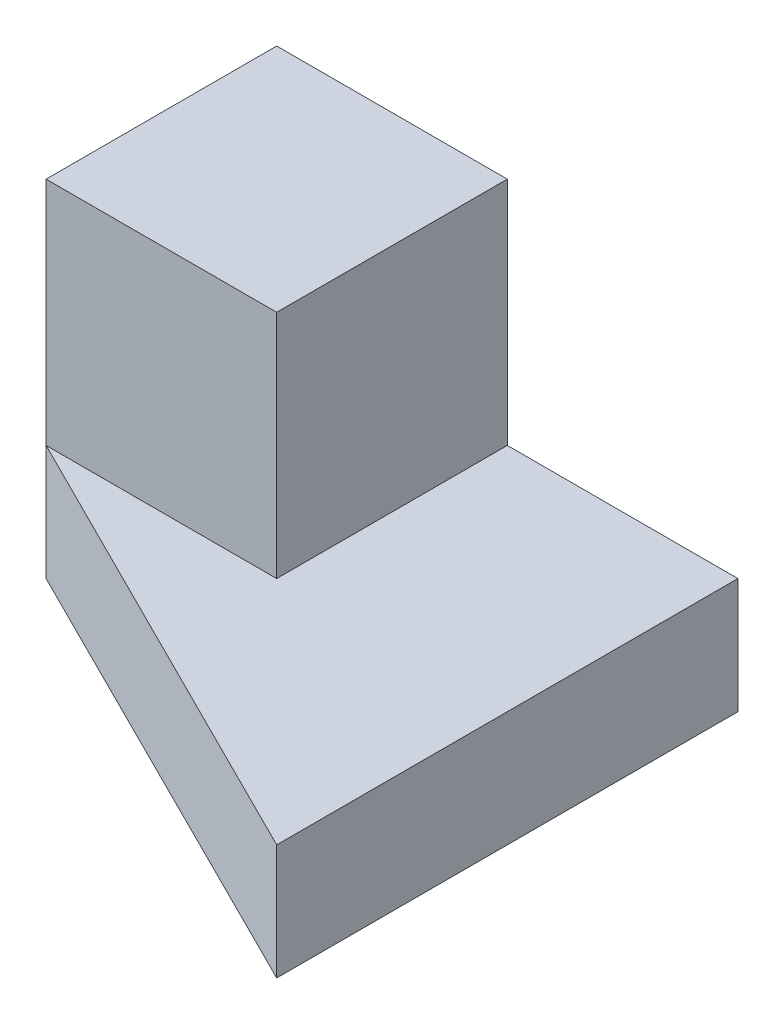
SolidWorks part; units mm, degrees
ref_plane "Front Plane" through (0, 0, 0) normal (0, 0, 1) x (1, 0, 0)
ref_plane "Top Plane" through (0, 0, 0) normal (0, 1, 0) x (1, 0, 0)
ref_plane "Right Plane" through (0, 0, 0) normal (1, 0, 0) x (0, 0, -1)
sketch "Sketch1" plane through (0, 0, 0) normal (0, 1, 0) x (1, 0, 0)
  line L0 (0, 0) -> (0, 40)
  line L1 (0, 40) -> (-40, 40)
  line L2 (-40, 40) -> (-40, 20)
  line L3 (-40, 20) -> (0, 0)
  dimension "D1" = 40
  dimension "D2" = 40
  dimension "D3" = 20
extrude "Boss-Extrude1" add sketch "Sketch1" along normal blind 10
sketch "Sketch2" plane through (0, 10, 0) normal (0, 1, 0) x (1, 0, 0)
  line L0 (-40, 20) -> (-40, 40)
  line L1 (-40, 40) -> (-20, 40)
  line L2 (0, 40) -> (-40, 40) construction
  line L3 (-20, 40) -> (-20, 20)
  line L4 (-20, 20) -> (-40, 20)
  dimension "D1" = 20
extrude "Boss-Extrude2" add sketch "Sketch2" along normal blind 20
